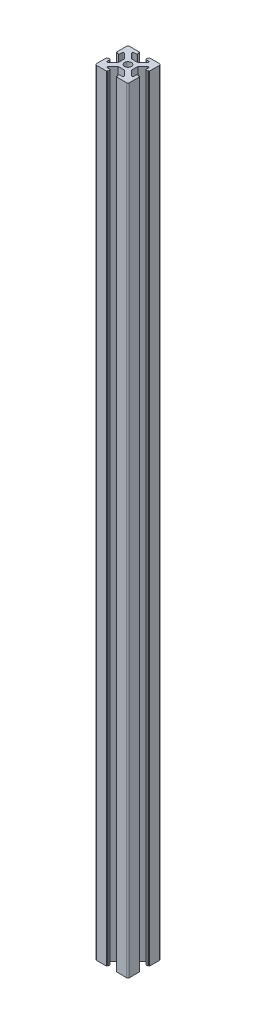
SolidWorks part; units mm, degrees
ref_plane "정면" through (0, 0, 0) normal (0, 0, 1) x (1, 0, 0)
ref_plane "윗면" through (0, 0, 0) normal (0, 1, 0) x (1, 0, 0)
ref_plane "우측면" through (0, 0, 0) normal (1, 0, 0) x (0, 0, -1)
sketch "스케치1" plane through (0, 0, 0) normal (0, 1, 0) x (1, 0, 0)
  line L0 (0, 4) -> (0, -4) construction
  line L1 (2, -4) -> (-2, -4)
  line L2 (-2, -4) -> (-5, -7)
  line L3 (-5, -7) -> (-5, -8) construction
  line L4 (-5, -8) -> (-2.6, -8) construction
  line L5 (-2.6, -8) -> (-2.6, -9.5) construction
  line L6 (-2.6, -9.5) -> (-3.1, -9.5)
  line L7 (-3.1, -9.5) -> (-3.1, -10)
  line L8 (-3.1, -10) -> (-9, -10)
  line L9 (-9, -10) -> (-9, -9) construction
  line L10 (-9, -10) -> (-10, -10) construction
  line L11 (-9, -9) -> (-10, -9) construction
  line L12 (-10, -10) -> (-10, -9) construction
  line L13 (3.1, -8) -> (3.1, -8.5) construction
  line L14 (2.6, -8.5) -> (3.1, -8.5) construction
  line L15 (2.6, -8) -> (2.6, -8.5) construction
  line L16 (-5, -7) -> (-5, -7.5)
  line L17 (-5, -8) -> (-4.5, -8) construction
  line L18 (-5, -8) -> (-5, -7.5) construction
  line L19 (-5, -7.5) -> (-4.5, -7.5) construction
  line L20 (-4.5, -8) -> (-4.5, -7.5) construction
  line L21 (-2.6, -9.5) -> (-2.6, -8.5)
  line L22 (-2.6, -8) -> (-3.1, -8) construction
  line L23 (-2.6, -8) -> (-2.6, -8.5) construction
  line L24 (-2.6, -8.5) -> (-3.1, -8.5) construction
  line L25 (-3.1, -8) -> (-3.1, -8.5) construction
  line L26 (-4.5, -8) -> (-3.1, -8)
  line L27 (2.6, -8) -> (3.1, -8) construction
  line L28 (4.5, -8) -> (4.5, -7.5) construction
  line L29 (5, -7.5) -> (4.5, -7.5) construction
  line L30 (5, -8) -> (5, -7.5) construction
  line L31 (5, -8) -> (4.5, -8) construction
  line L32 (10, -10) -> (10, -9) construction
  line L33 (9, -9) -> (10, -9) construction
  line L34 (9, -10) -> (10, -10) construction
  line L35 (9, -10) -> (9, -9) construction
  line L36 (2.6, -8) -> (2.6, -9.5) construction
  line L37 (5, -8) -> (2.6, -8) construction
  line L38 (5, -7) -> (5, -8) construction
  line L39 (4.5, -8) -> (3.1, -8)
  line L40 (2.6, -9.5) -> (2.6, -8.5)
  line L41 (5, -7) -> (5, -7.5)
  line L42 (3.1, -10) -> (9, -10)
  line L43 (3.1, -9.5) -> (3.1, -10)
  line L44 (2.6, -9.5) -> (3.1, -9.5)
  line L45 (2, -4) -> (5, -7)
  line L46 (-4, -2) -> (-4, 2)
  line L47 (-4, 2) -> (-7, 5)
  line L48 (-9.5, 2.6) -> (-9.5, 3.1)
  line L49 (-9.5, 3.1) -> (-10, 3.1)
  line L50 (-10, 3.1) -> (-10, 9)
  line L51 (-7, 5) -> (-7.5, 5)
  line L52 (-9.5, 2.6) -> (-8.5, 2.6)
  line L53 (-8, 4.5) -> (-8, 3.1)
  line L54 (-8, -4.5) -> (-8, -3.1)
  line L55 (-9.5, -2.6) -> (-8.5, -2.6)
  line L56 (-7, -5) -> (-7.5, -5)
  line L57 (-10, -3.1) -> (-10, -9)
  line L58 (-9.5, -3.1) -> (-10, -3.1)
  line L59 (-9.5, -2.6) -> (-9.5, -3.1)
  line L60 (-4, -2) -> (-7, -5)
  line L61 (4, 0) -> (-4, 0) construction
  line L62 (-7, 5) -> (-8, 5) construction
  line L63 (-8, 5) -> (-8, 2.6) construction
  line L64 (-8, 2.6) -> (-9.5, 2.6) construction
  line L65 (-10, 9) -> (-9, 9) construction
  line L66 (-10, 9) -> (-10, 10) construction
  line L67 (-9, 9) -> (-9, 10) construction
  line L68 (-10, 10) -> (-9, 10) construction
  line L69 (-8, -3.1) -> (-8.5, -3.1) construction
  line L70 (-8.5, -2.6) -> (-8.5, -3.1) construction
  line L71 (-8, -2.6) -> (-8.5, -2.6) construction
  line L72 (-8, 5) -> (-8, 4.5) construction
  line L73 (-8, 5) -> (-7.5, 5) construction
  line L74 (-7.5, 5) -> (-7.5, 4.5) construction
  line L75 (-8, 4.5) -> (-7.5, 4.5) construction
  line L76 (-8, 2.6) -> (-8, 3.1) construction
  line L77 (-8, 2.6) -> (-8.5, 2.6) construction
  line L78 (-8.5, 2.6) -> (-8.5, 3.1) construction
  line L79 (-8, 3.1) -> (-8.5, 3.1) construction
  line L80 (-8, -2.6) -> (-8, -3.1) construction
  line L81 (-8, -4.5) -> (-7.5, -4.5) construction
  line L82 (-7.5, -5) -> (-7.5, -4.5) construction
  line L83 (-8, -5) -> (-7.5, -5) construction
  line L84 (-8, -5) -> (-8, -4.5) construction
  line L85 (-10, -10) -> (-9, -10) construction
  line L86 (-9, -9) -> (-9, -10) construction
  line L87 (-10, -9) -> (-10, -10) construction
  line L88 (-10, -9) -> (-9, -9) construction
  line L89 (-8, -2.6) -> (-9.5, -2.6) construction
  line L90 (-8, -5) -> (-8, -2.6) construction
  line L91 (-7, -5) -> (-8, -5) construction
  line L92 (-2, 4) -> (2, 4)
  line L93 (2, 4) -> (5, 7)
  line L94 (2.6, 9.5) -> (3.1, 9.5)
  line L95 (3.1, 9.5) -> (3.1, 10)
  line L96 (3.1, 10) -> (9, 10)
  line L97 (5, 7) -> (5, 7.5)
  line L98 (2.6, 9.5) -> (2.6, 8.5)
  line L99 (4.5, 8) -> (3.1, 8)
  line L100 (-4.5, 8) -> (-3.1, 8)
  line L101 (-2.6, 9.5) -> (-2.6, 8.5)
  line L102 (-5, 7) -> (-5, 7.5)
  line L103 (-3.1, 10) -> (-9, 10)
  line L104 (-3.1, 9.5) -> (-3.1, 10)
  line L105 (-2.6, 9.5) -> (-3.1, 9.5)
  line L106 (-2, 4) -> (-5, 7)
  line L107 (0, -4) -> (0, 4) construction
  line L108 (5, 7) -> (5, 8) construction
  line L109 (5, 8) -> (2.6, 8) construction
  line L110 (2.6, 8) -> (2.6, 9.5) construction
  line L111 (9, 10) -> (9, 9) construction
  line L112 (9, 10) -> (10, 10) construction
  line L113 (9, 9) -> (10, 9) construction
  line L114 (10, 10) -> (10, 9) construction
  line L115 (-3.1, 8) -> (-3.1, 8.5) construction
  line L116 (-2.6, 8.5) -> (-3.1, 8.5) construction
  line L117 (-2.6, 8) -> (-2.6, 8.5) construction
  line L118 (5, 8) -> (4.5, 8) construction
  line L119 (5, 8) -> (5, 7.5) construction
  line L120 (5, 7.5) -> (4.5, 7.5) construction
  line L121 (4.5, 8) -> (4.5, 7.5) construction
  line L122 (2.6, 8) -> (3.1, 8) construction
  line L123 (2.6, 8) -> (2.6, 8.5) construction
  line L124 (2.6, 8.5) -> (3.1, 8.5) construction
  line L125 (3.1, 8) -> (3.1, 8.5) construction
  line L126 (-2.6, 8) -> (-3.1, 8) construction
  line L127 (-4.5, 8) -> (-4.5, 7.5) construction
  line L128 (-5, 7.5) -> (-4.5, 7.5) construction
  line L129 (-5, 8) -> (-5, 7.5) construction
  line L130 (-5, 8) -> (-4.5, 8) construction
  line L131 (-10, 10) -> (-10, 9) construction
  line L132 (-9, 9) -> (-10, 9) construction
  line L133 (-9, 10) -> (-10, 10) construction
  line L134 (-9, 10) -> (-9, 9) construction
  line L135 (-2.6, 8) -> (-2.6, 9.5) construction
  line L136 (-5, 8) -> (-2.6, 8) construction
  line L137 (-5, 7) -> (-5, 8) construction
  line L138 (4, 2) -> (4, -2)
  line L139 (4, -2) -> (7, -5)
  line L140 (9.5, -2.6) -> (9.5, -3.1)
  line L141 (9.5, -3.1) -> (10, -3.1)
  line L142 (10, -3.1) -> (10, -9)
  line L143 (7, -5) -> (7.5, -5)
  line L144 (9.5, -2.6) -> (8.5, -2.6)
  line L145 (8, -4.5) -> (8, -3.1)
  line L146 (8, 4.5) -> (8, 3.1)
  line L147 (9.5, 2.6) -> (8.5, 2.6)
  line L148 (7, 5) -> (7.5, 5)
  line L149 (10, 3.1) -> (10, 9)
  line L150 (9.5, 3.1) -> (10, 3.1)
  line L151 (9.5, 2.6) -> (9.5, 3.1)
  line L152 (4, 2) -> (7, 5)
  line L153 (-4, 0) -> (4, 0) construction
  line L154 (7, -5) -> (8, -5) construction
  line L155 (8, -5) -> (8, -2.6) construction
  line L156 (8, -2.6) -> (9.5, -2.6) construction
  line L157 (10, -9) -> (9, -9) construction
  line L158 (10, -9) -> (10, -10) construction
  line L159 (9, -9) -> (9, -10) construction
  line L160 (10, -10) -> (9, -10) construction
  line L161 (8, 3.1) -> (8.5, 3.1) construction
  line L162 (8.5, 2.6) -> (8.5, 3.1) construction
  line L163 (8, 2.6) -> (8.5, 2.6) construction
  line L164 (8, -5) -> (8, -4.5) construction
  line L165 (8, -5) -> (7.5, -5) construction
  line L166 (7.5, -5) -> (7.5, -4.5) construction
  line L167 (8, -4.5) -> (7.5, -4.5) construction
  line L168 (8, -2.6) -> (8, -3.1) construction
  line L169 (8, -2.6) -> (8.5, -2.6) construction
  line L170 (8.5, -2.6) -> (8.5, -3.1) construction
  line L171 (8, -3.1) -> (8.5, -3.1) construction
  line L172 (8, 2.6) -> (8, 3.1) construction
  line L173 (8, 4.5) -> (7.5, 4.5) construction
  line L174 (7.5, 5) -> (7.5, 4.5) construction
  line L175 (8, 5) -> (7.5, 5) construction
  line L176 (8, 5) -> (8, 4.5) construction
  line L177 (10, 10) -> (9, 10) construction
  line L178 (9, 9) -> (9, 10) construction
  line L179 (10, 9) -> (10, 10) construction
  line L180 (10, 9) -> (9, 9) construction
  line L181 (8, 2.6) -> (9.5, 2.6) construction
  line L182 (8, 5) -> (8, 2.6) construction
  line L183 (7, 5) -> (8, 5) construction
  circle A0 centre (0, 0) radius 2.1
  arc A1 (-5, -7.5) -> (-4.5, -8) centre (-4.5, -7.5) ccw
  arc A2 (-3.1, -8) -> (-2.6, -8.5) centre (-3.1, -8.5) cw
  arc A3 (-9, -10) -> (-9.7071, -9.7071) centre (-9, -9) cw
  arc A4 (9, -10) -> (9.7071, -9.7071) centre (9, -9) ccw
  arc A5 (3.1, -8) -> (2.6, -8.5) centre (3.1, -8.5) ccw
  arc A6 (5, -7.5) -> (4.5, -8) centre (4.5, -7.5) cw
  arc A7 (-7.5, 5) -> (-8, 4.5) centre (-7.5, 4.5) ccw
  arc A8 (-8, 3.1) -> (-8.5, 2.6) centre (-8.5, 3.1) cw
  arc A9 (-10, 9) -> (-9.7071, 9.7071) centre (-9, 9) cw
  arc A10 (-10, -9) -> (-9.7071, -9.7071) centre (-9, -9) ccw
  arc A11 (-8, -3.1) -> (-8.5, -2.6) centre (-8.5, -3.1) ccw
  arc A12 (-7.5, -5) -> (-8, -4.5) centre (-7.5, -4.5) cw
  arc A13 (5, 7.5) -> (4.5, 8) centre (4.5, 7.5) ccw
  arc A14 (3.1, 8) -> (2.6, 8.5) centre (3.1, 8.5) cw
  arc A15 (9, 10) -> (9.7071, 9.7071) centre (9, 9) cw
  arc A16 (-9, 10) -> (-9.7071, 9.7071) centre (-9, 9) ccw
  arc A17 (-3.1, 8) -> (-2.6, 8.5) centre (-3.1, 8.5) ccw
  arc A18 (-5, 7.5) -> (-4.5, 8) centre (-4.5, 7.5) cw
  arc A19 (7.5, -5) -> (8, -4.5) centre (7.5, -4.5) ccw
  arc A20 (8, -3.1) -> (8.5, -2.6) centre (8.5, -3.1) cw
  arc A21 (10, -9) -> (9.7071, -9.7071) centre (9, -9) cw
  arc A22 (10, 9) -> (9.7071, 9.7071) centre (9, 9) ccw
  arc A23 (8, 3.1) -> (8.5, 2.6) centre (8.5, 3.1) ccw
  arc A24 (7.5, 5) -> (8, 4.5) centre (7.5, 4.5) cw
  point P6 (0, 0)
  point P9 (0, -4)
  point P52 (-4, 0)
  point P92 (0, 4)
  point P132 (4, 0)
  point P167 (0, 0)
  dimension "D1" = 4.2
  dimension "D9" = 1
  dimension "D2" = 4
  dimension "D3" = 4
  dimension "D4" = 3
  dimension "D5" = 1
  dimension "D6" = 2
  dimension "D7" = 2.6
  dimension "D8" = 3.1
  dimension "D10" = 1
  dimension "D11" = 0.5
  dimension "D12" = 0.5
  dimension "D13" = 0.5
  dimension "D14" = 5
  dimension "D15" = 45
  dimension "D16" = 1
  dimension "D17" = 10
  dimension "D18" = 4
extrude "보스-돌출1" add sketch "스케치1" along normal blind 470
